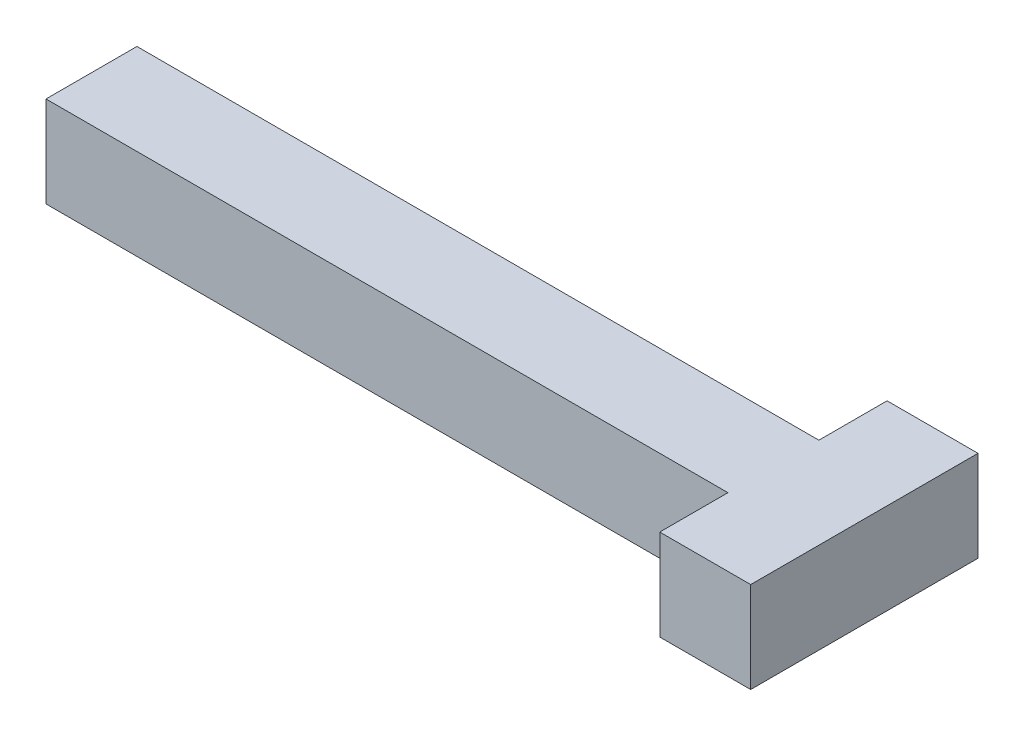
SolidWorks part; units mm, degrees
ref_plane "Front Plane" through (0, 0, 0) normal (0, 0, 1) x (1, 0, 0)
ref_plane "Top Plane" through (0, 0, 0) normal (0, 1, 0) x (1, 0, 0)
ref_plane "Right Plane" through (0, 0, 0) normal (1, 0, 0) x (0, 0, -1)
sketch "Sketch1" plane through (0, 0, 0) normal (0, 1, 0) x (1, 0, 0)
  line L1 (-7.5, -1) -> (7.5, -1)
  line L2 (-7.5, -1) -> (-7.5, 1)
  line L3 (-7.5, 1) -> (7.5, 1)
  line L4 (7.5, -1) -> (7.5, 1)
  line L5 (-7.5, -1) -> (7.5, 1) construction
  line L6 (-7.5, 1) -> (7.5, -1) construction
  line L7 (7.5, 2.5) -> (9.5, 2.5)
  line L8 (7.5, 2.5) -> (7.5, -2.5)
  line L9 (7.5, -2.5) -> (9.5, -2.5)
  line L10 (9.5, 2.5) -> (9.5, -2.5)
  point P0 (0, 0)
  point P10 (9.5, 0)
  dimension "D1" = 15
  dimension "D2" = 2
  dimension "D3" = 5
  dimension "D4" = 2
  dimension "D5" = 0
  dimension "D6" = 2
extrude "Boss-Extrude1" add sketch "Sketch1" along normal blind 2 contours L1 L4 L3 L2 | L10 L7 L8 L4 L9
